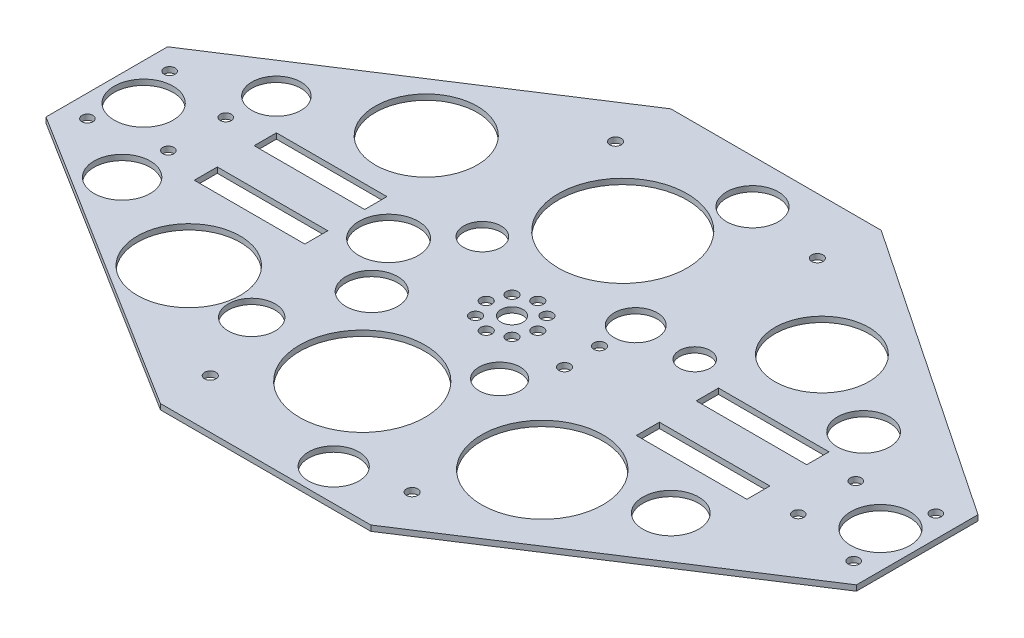
SolidWorks part; units mm, degrees
ref_plane "前视基准面" through (0, 0, 0) normal (0, 0, 1) x (1, 0, 0)
ref_plane "上视基准面" through (0, 0, 0) normal (0, 1, 0) x (1, 0, 0)
ref_plane "右视基准面" through (0, 0, 0) normal (1, 0, 0) x (0, 0, -1)
sketch "草图1" plane through (0, 0, 0) normal (0, 1, 0) x (1, 0, 0)
  line L0 (109.9962, -33) -> (109.9962, 0) construction
  line L1 (0, -33) -> (82.8926, -84.8369)
  line L2 (0, 0) -> (0, -33)
  line L3 (0, 0) -> (82.8926, 53.7138)
  line L4 (219.9923, 0) -> (219.9923, -33)
  line L5 (185, -5.45) -> (185, -11.5)
  line L6 (155, -5.45) -> (185, -5.45)
  line L7 (65, -16.5) -> (65, -11.5) construction
  line L8 (185, -27.75) -> (155, -27.75)
  line L9 (185, -21.5) -> (155, -21.5)
  line L10 (65, -16.5) -> (65, -21.5) construction
  line L11 (65, -21.5) -> (35, -21.5)
  line L12 (155, -11.5) -> (155, -5.45)
  line L13 (185, -11.5) -> (155, -11.5)
  line L14 (185, -21.5) -> (185, -27.75)
  line L15 (155, -21.5) -> (155, -27.75)
  line L16 (35, -21.5) -> (35, -27.75)
  line L17 (35, -27.75) -> (65, -27.75)
  line L18 (65, -27.75) -> (65, -21.5)
  line L19 (65, -11.5) -> (35, -11.5)
  line L20 (35, -11.5) -> (35, -5.45)
  line L21 (35, -5.45) -> (65, -5.45)
  line L22 (65, -5.45) -> (65, -11.5)
  line L23 (109.9962, -16.5) -> (116.9962, -16.5) construction
  line L24 (116.9962, -16.5) -> (116.9962, -23.5) construction
  line L25 (116.9962, -23.5) -> (109.9962, -23.5) construction
  line L26 (109.9962, -23.5) -> (102.9962, -23.5) construction
  line L27 (102.9962, -23.5) -> (102.9962, -16.5) construction
  line L28 (102.9962, -16.5) -> (109.9962, -16.5) construction
  line L29 (116.9962, -16.5) -> (116.9962, -9.5) construction
  line L30 (116.9962, -9.5) -> (109.9962, -9.5) construction
  line L31 (109.9962, -9.5) -> (102.9962, -9.5) construction
  line L32 (102.9962, -9.5) -> (102.9962, -16.5) construction
  line L33 (114.9459, -21.4497) -> (129.1959, -21.4497) construction
  line L34 (109.9962, -16.5) -> (116.9962, -23.5) construction
  line L35 (109.9962, -16.5) -> (116.9962, -9.5) construction
  line L36 (109.9962, -16.5) -> (102.9962, -9.5) construction
  line L37 (109.9962, -16.5) -> (114.9459, -21.4497) construction
  line L38 (109.9962, -16.5) -> (105.0464, -21.4497) construction
  line L39 (109.9962, -16.5) -> (105.0464, -11.5503) construction
  line L40 (109.7926, -16.7035) -> (114.7424, -11.7538) construction
  line L41 (109.9962, -16.5) -> (137.8962, -16.5) construction
  line L42 (114.7424, -11.7538) -> (128.9924, -11.7538) construction
  line L43 (109.9962, -16.5) -> (83.0962, -16.5) construction
  line L44 (137.8962, -16.5) -> (137.8962, -71.5) construction
  line L45 (137.8962, -16.5) -> (137.8962, 38.5) construction
  line L46 (83.0962, -16.5) -> (83.0962, 38.5) construction
  line L48 (82.8926, -84.8369) -> (139.9962, -84.8369)
  line L49 (139.9962, -84.8369) -> (219.9923, -33)
  line L50 (82.8926, 53.7138) -> (139.9962, 53.7138)
  line L51 (139.9962, 53.7138) -> (219.9923, 0)
  line L52 (83.0962, -16.5) -> (83.0962, -71.5) construction
  circle A0 centre (6, -27.75) radius 1.5
  circle A1 centre (6, -5.45) radius 1.5
  circle A2 centre (24.5, -8.7) radius 1.5
  circle A3 centre (24.5, -24.3) radius 1.5
  circle A4 centre (195.5, -8.7) radius 1.5
  circle A5 centre (195.5, -24.3) radius 1.5
  circle A6 centre (214, -27.75) radius 1.5
  circle A7 centre (214, -5.45) radius 1.5
  circle A8 centre (105.0464, -21.4497) radius 1.55
  circle A9 centre (114.9459, -21.4497) radius 1.55
  circle A10 centre (10, -16.5) radius 8
  circle A11 centre (210, -16.5) radius 8
  circle A12 centre (114.7424, -11.7538) radius 1.55
  circle A13 centre (83.0962, 38.5) radius 1.55
  circle A14 centre (105.0464, -11.5503) radius 1.55
  circle A15 centre (102.9962, -16.5) radius 1.55
  circle A16 centre (109.9962, -23.5) radius 1.555
  circle A17 centre (116.9962, -16.5) radius 1.55
  circle A18 centre (109.9962, -9.5) radius 1.55
  circle A19 centre (109.9962, -16.5) radius 3
  circle A20 centre (129.1959, -21.4497) radius 1.55
  circle A21 centre (128.9924, -11.7538) radius 1.55
  circle A22 centre (137.8962, 38.5) radius 1.55
  circle A23 centre (137.8962, -71.5) radius 1.55
  circle A24 centre (83.0962, -71.5) radius 1.55
  circle A25 centre (105.0464, 18.5037) radius 17.4862
  circle A26 centre (105.0464, -52.199) radius 17.0205
  circle A27 centre (150.2996, -48.5858) radius 16.4672
  circle A28 centre (55.9789, 14.2349) radius 13.8437
  circle A29 centre (161.159, 16.4602) radius 12.7633
  circle A30 centre (54.3447, -48.5858) radius 13.9728
  circle A31 centre (116.9962, 41.7776) radius 7.0272
  circle A32 centre (75.0419, -15.0504) radius 8.0542
  circle A33 centre (85.2374, -29.8064) radius 7.0295
  circle A34 centre (87.3656, -1.9117) radius 5.0648
  circle A35 centre (128.9924, -1.9117) radius 5.8476
  circle A36 centre (145.0206, -1.9117) radius 4.1722
  circle A37 centre (185, 3.9359) radius 7.0805
  circle A38 centre (177.9195, -41.3216) radius 7.5695
  circle A39 centre (26.3855, 3.1531) radius 6.6733
  circle A40 centre (24.5, -36.8359) radius 7.6332
  circle A41 centre (75.0419, -52.199) radius 6.379
  circle A42 centre (121.2065, -76.1071) radius 6.8425
  circle A43 centre (123.1448, -33) radius 5.5892
extrude "凸台-拉伸1" add sketch "草图1" along normal blind 1.5
